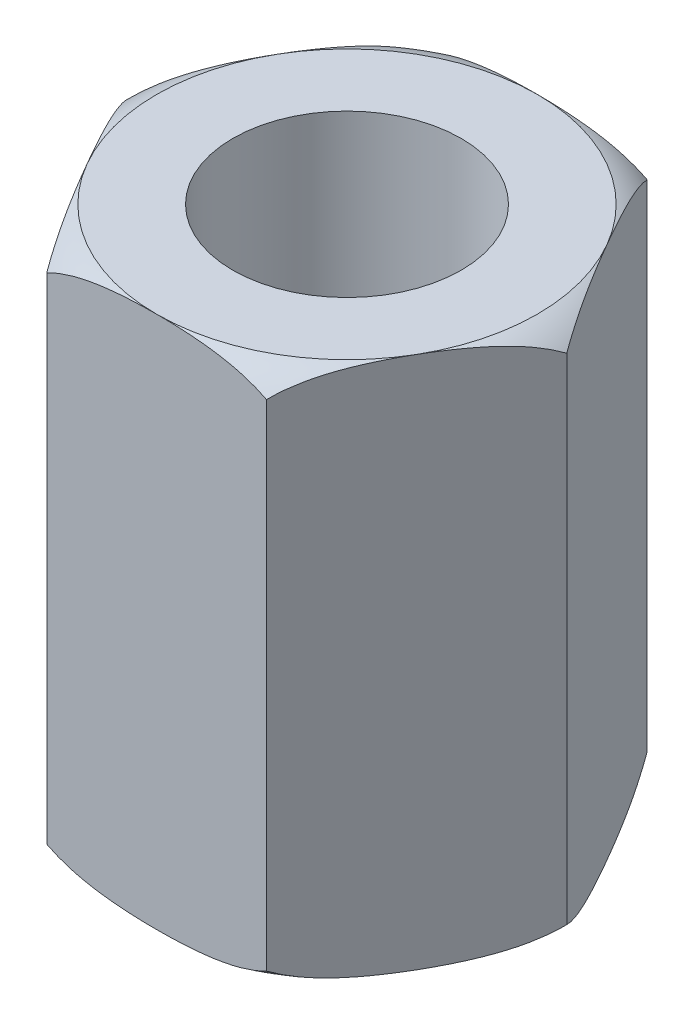
SolidWorks part; units mm, degrees
material "1060 Alloy"
ref_plane "Front Plane" through (0, 0, 0) normal (0, 0, 1) x (1, 0, 0)
ref_plane "Top Plane" through (0, 0, 0) normal (0, 1, 0) x (1, 0, 0)
ref_plane "Right Plane" through (0, 0, 0) normal (1, 0, 0) x (0, 0, -1)
sketch "Sketch1" plane through (0, 0, 0) normal (0, 1, 0) x (1, 0, 0)
  line L0 (-2.8868, 0) -> (2.8868, 0) construction
  line L1 (2.8868, 0) -> (1.4434, 2.5)
  line L2 (1.4434, 2.5) -> (-1.4434, 2.5)
  line L3 (-1.4434, 2.5) -> (-2.8868, 0)
  line L4 (-2.8868, 0) -> (-1.4434, -2.5)
  line L5 (-1.4434, -2.5) -> (1.4434, -2.5)
  line L6 (1.4434, -2.5) -> (2.8868, 0)
  circle A0 centre (0, 0) radius 2.5 construction
  circle A1 centre (0, 0) radius 1.5
  circle A2 centre (0, 0) radius 2.5 construction
  dimension "D2" = 3
  dimension "D1" = 5
extrude "Boss-Extrude1" add sketch "Sketch1" along normal blind 7
sketch "Sketch3" plane through (0, 0, 0) normal (1, 0, 0) x (0, 0, -1)
  line L0 (-1.5, 7) -> (-2.5, 7)
  line L1 (-2.5, 7) -> (-2.5, 6.7226)
  line L2 (0, 7) -> (0, 0) construction
  line L3 (-2.5, 7) -> (-2.5, 0) construction
  line L4 (0, 7.4268) -> (0, -1.5368) construction
  circle A0 centre (0, -0.3485) radius 7.5
  dimension "D1" = 15
sketch "Sketch5" plane through (0, 0, 0) normal (0, 0, 1) x (1, 0, 0)
  line L0 (-2.5, 0) -> (-2.8868, 0)
  line L1 (-2.8868, 0) -> (2.8868, 0) construction
  line L2 (2.5, 0) -> (-2.5, 0) construction
  line L3 (-2.8868, 0) -> (-2.8868, 0.25)
  line L4 (-2.8868, 7) -> (-2.8868, 0) construction
  line L5 (-2.8868, 3.5) -> (2.8868, 3.5) construction
  line L6 (2.8868, 7) -> (2.8868, 0) construction
  line L7 (-2.8868, 7) -> (-2.8868, 6.75)
  line L8 (-2.5, 7) -> (-2.8868, 7)
  arc A0 (-2.8868, 0.25) -> (-2.5, 0) centre (-2.1651, 0.9423) ccw
  arc A1 (-2.8868, 6.75) -> (-2.5, 7) centre (-2.1651, 6.0577) cw
  dimension "D1" = 1
  dimension "D2" = 0.25
revolve "Cut-Revolve4" cut sketch "Sketch5" angle 360 about L4
